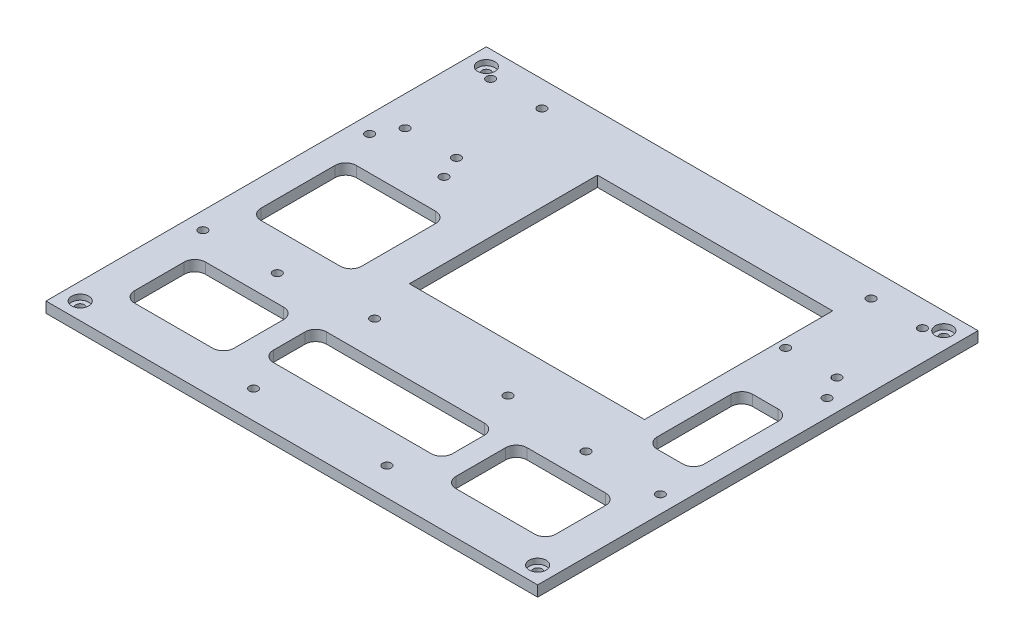
SolidWorks part; units mm, degrees
material "Custom Plastic"
ref_plane "Front Plane" through (0, 0, 0) normal (0, 0, 1) x (1, 0, 0)
ref_plane "Top Plane" through (0, 0, 0) normal (0, 1, 0) x (1, 0, 0)
ref_plane "Right Plane" through (0, 0, 0) normal (1, 0, 0) x (0, 0, -1)
sketch "Sketch1" plane through (0, 0, 0) normal (0, 1, 0) x (1, 0, 0)
  line L1 (-59.5, -51.5) -> (59.5, -51.5)
  line L2 (-59.5, -51.5) -> (-59.5, 51.5)
  line L3 (-59.5, 51.5) -> (59.5, 51.5)
  line L4 (59.5, -51.5) -> (59.5, 51.5)
  line L5 (-59.5, -51.5) -> (59.5, 51.5) construction
  line L6 (-59.5, 51.5) -> (59.5, -51.5) construction
  point P0 (0, 0)
  dimension "D1" = 119
  dimension "D2" = 103
extrude "Boss-Extrude1" add sketch "Sketch1" along normal blind 2.5
sketch "Sketch3" plane through (0, 2.5, 0) normal (0, 1, 0) x (1, 0, 0)
  line L0 (-59.5, -51.5) -> (59.5, -51.5) construction
  line L1 (-18.5, -5.5) -> (36.5, -5.5)
  line L2 (-18.5, -5.5) -> (-18.5, 38.5)
  line L3 (-18.5, 38.5) -> (36.5, 38.5)
  line L4 (36.5, -5.5) -> (36.5, 38.5)
  line L5 (-18.5, -5.5) -> (36.5, 38.5) construction
  line L6 (-18.5, 38.5) -> (36.5, -5.5) construction
  line L7 (-59.5, 51.5) -> (-59.5, -51.5) construction
  point P0 (9, 16.5)
  dimension "D1" = 46
  dimension "D2" = 41
  dimension "D3" = 44
  dimension "D4" = 55
extrude "Cut-Extrude2" cut sketch "Sketch3" against normal blind 10
sketch "Sketch4" plane through (-59.5, 0, 0) normal (-1, 0, 0) x (0, 0, 1)
  line L4 (-51.5, 0) -> (51.5, 0)
  line L5 (51.5, 0) -> (51.5, 2.5)
  line L6 (51.5, 2.5) -> (-51.5, 2.5)
  line L7 (-51.5, 2.5) -> (-51.5, 0)
  line L8 (-51.5, 0) -> (51.5, 0)
  line L9 (51.5, 0) -> (51.5, 2.5)
  line L10 (51.5, 2.5) -> (-51.5, 2.5)
  line L11 (-51.5, 2.5) -> (-51.5, 0)
  dimension "D1" = 0
extrude "Boss-Extrude2" add sketch "Sketch4" along normal blind 1.5
sketch "Sketch5" plane through (59.5, 0, 0) normal (1, 0, 0) x (0, 0, -1)
  line L4 (-51.5, 0) -> (51.5, 0)
  line L5 (51.5, 0) -> (51.5, 2.5)
  line L6 (51.5, 2.5) -> (-51.5, 2.5)
  line L7 (-51.5, 2.5) -> (-51.5, 0)
  line L8 (-51.5, 0) -> (51.5, 0)
  line L9 (51.5, 0) -> (51.5, 2.5)
  line L10 (51.5, 2.5) -> (-51.5, 2.5)
  line L11 (-51.5, 2.5) -> (-51.5, 0)
  dimension "D1" = 0
extrude "Boss-Extrude3" add sketch "Sketch5" along normal blind 1.5
sketch "Sketch6" plane through (-61, 0, 0) normal (-1, 0, 0) x (0, 0, 1)
  line L4 (-51.5, 2.5) -> (-51.5, 0)
  line L5 (-51.5, 0) -> (51.5, 0)
  line L6 (51.5, 0) -> (51.5, 2.5)
  line L7 (51.5, 2.5) -> (-51.5, 2.5)
  line L8 (-51.5, 2.5) -> (-51.5, 0)
  line L9 (-51.5, 0) -> (51.5, 0)
  line L10 (51.5, 0) -> (51.5, 2.5)
  line L11 (51.5, 2.5) -> (-51.5, 2.5)
  dimension "D1" = 0
extrude "Cut-Extrude3" cut sketch "Sketch6" against normal blind 3.5
sketch "Sketch7" plane through (61, 0, 0) normal (1, 0, 0) x (0, 0, -1)
  line L4 (-51.5, 2.5) -> (-51.5, 0)
  line L5 (-51.5, 0) -> (51.5, 0)
  line L6 (51.5, 0) -> (51.5, 2.5)
  line L7 (51.5, 2.5) -> (-51.5, 2.5)
  line L8 (-51.5, 2.5) -> (-51.5, 0)
  line L9 (-51.5, 0) -> (51.5, 0)
  line L10 (51.5, 0) -> (51.5, 2.5)
  line L11 (51.5, 2.5) -> (-51.5, 2.5)
  dimension "D1" = 0
extrude "Cut-Extrude4" cut sketch "Sketch7" against normal blind 3.5
sketch "Sketch8" plane through (0, 2.5, 0) normal (0, 1, 0) x (1, 0, 0)
  line L0 (-57.5, -51.5) -> (-57.5, 51.5) construction
  line L1 (-57.5, -51.5) -> (57.5, -51.5) construction
  line L3 (0, 59.9293) -> (0, -77.2132) construction
  circle A0 centre (-15.5, -44.96) radius 1
  circle A1 centre (15.7, -44.96) radius 1
  circle A2 centre (-15.5, -16.63) radius 1
  circle A3 centre (15.7, -16.63) radius 1
  circle A4 centre (-53.5, -18.81) radius 1
  circle A5 centre (-36.1, -18.81) radius 1
  circle A6 centre (-53.5, 20.19) radius 1
  circle A7 centre (-36.1, 20.19) radius 1
  circle A8 centre (36.1, -18.81) radius 1
  circle A9 centre (53.5, -18.81) radius 1
  circle A10 centre (53.5, 20.19) radius 1
  dimension "D1" = 2
  dimension "D2" = 2
  dimension "D7" = 2
  dimension "D8" = 2
  dimension "D13" = 2
  dimension "D14" = 2
  dimension "D15" = 2
  dimension "D16" = 2
  dimension "D3" = 42
  dimension "D4" = 31.2
  dimension "D5" = 6.54
  dimension "D6" = 6.54
  dimension "D9" = 28.33
  dimension "D10" = 28.33
  dimension "D11" = 32.69
  dimension "D12" = 4
  dimension "D17" = 4
  dimension "D18" = 39
  dimension "D19" = 17.4
extrude "Cut-Extrude5" cut sketch "Sketch8" against normal blind 10
sketch "Sketch9" plane through (0, 2.5, 0) normal (0, 1, 0) x (1, 0, 0)
  line L0 (-57.5, -51.5) -> (-57.5, 51.5) construction
  line L1 (57.5, 51.5) -> (-57.5, 51.5) construction
  circle A0 centre (-53.5, 47.5) radius 1
  circle A1 centre (53.5, -47.5) radius 1
  circle A2 centre (53.5, 47.5) radius 1
  circle A3 centre (-53.5, -47.5) radius 1
  point P10 (0, 0)
  dimension "D3" = 2
  dimension "D5" = 2
  dimension "D6" = 2
  dimension "D1" = 4
  dimension "D2" = 4
  dimension "D4" = 2
extrude "Cut-Extrude6" cut sketch "Sketch9" against normal blind 10
sketch "Sketch10" plane through (0, 2.5, 0) normal (0, 1, 0) x (1, 0, 0)
  circle A0 centre (-53.5, 47.5) radius 2
  circle A1 centre (-53.5, -47.5) radius 2
  circle A2 centre (53.5, -47.5) radius 2
  circle A3 centre (53.5, 47.5) radius 2
  dimension "D1" = 4
  dimension "D2" = 4
  dimension "D3" = 4
  dimension "D4" = 4
extrude "Cut-Extrude7" cut sketch "Sketch10" against normal blind 1.25
sketch "Sketch11" plane through (0, 2.5, 0) normal (0, 1, 0) x (1, 0, 0)
  line L0 (-57.5, 51.5) -> (-57.5, -51.5) construction
  line L1 (-57.5, -51.5) -> (-57.5, 51.5) construction
  line L2 (57.5, 51.5) -> (-57.5, 51.5) construction
  line L4 (0, 60.3804) -> (0, 0) construction
  circle A0 centre (-50.5, 45.5) radius 1
  circle A1 centre (-50.5, 25.5) radius 1
  circle A2 centre (-38.5, 45.5) radius 1
  circle A3 centre (-38.5, 25.5) radius 1
  circle A4 centre (50.5, 25.5) radius 1
  circle A5 centre (38.5, 25.5) radius 1
  circle A6 centre (38.5, 45.5) radius 1
  circle A7 centre (50.5, 45.5) radius 1
  dimension "D1" = 2
  dimension "D2" = 2
  dimension "D3" = 2
  dimension "D4" = 2
  dimension "D5" = 7
  dimension "D6" = 7
  dimension "D7" = 12
  dimension "D9" = 6
  dimension "D10" = 20
extrude "Cut-Extrude8" cut sketch "Sketch11" against normal blind 11
sketch "Sketch12" plane through (0, 2.5, 0) normal (0, 1, 0) x (1, 0, 0)
  line L0 (-46.7391, -24.9455) -> (-28.4571, -24.9455)
  line L1 (-48.6757, -10.0359) -> (-30.1363, -10.0359)
  line L2 (-51.1757, -7.5359) -> (-51.1757, 9.7595)
  line L3 (-48.6757, 12.2595) -> (-30.1363, 12.2595)
  line L4 (-27.6363, -7.5359) -> (-27.6363, 9.7595)
  line L5 (-51.1757, -10.0359) -> (-27.6363, 12.2595) construction
  line L6 (-51.1757, 12.2595) -> (-27.6363, -10.0359) construction
  line L7 (-25.9571, -27.4455) -> (-25.9571, -39.0653)
  line L8 (-28.4571, -41.5653) -> (-46.7391, -41.5653)
  line L9 (-49.2391, -39.0653) -> (-49.2391, -27.4455)
  line L10 (-20.9571, -27.4455) -> (-20.9571, -34.8668)
  line L11 (-18.4571, -37.3668) -> (18.4571, -37.3668)
  line L12 (20.9571, -34.8668) -> (20.9571, -27.4455)
  line L13 (18.4571, -24.9455) -> (-18.4571, -24.9455)
  line L14 (28.4571, -41.5653) -> (46.8503, -41.5653)
  line L15 (49.3503, -39.0653) -> (49.3503, -27.4455)
  line L16 (46.8503, -24.9455) -> (28.4571, -24.9455)
  line L17 (25.9571, -27.4455) -> (25.9571, -39.0653)
  line L18 (0, 20.449) -> (0, -71.2445) construction
  line L19 (41.5, 9.7595) -> (41.5, -7.5359)
  line L20 (44, -10.0359) -> (50, -10.0359)
  line L21 (52.5, -7.5359) -> (52.5, 9.7595)
  line L22 (50, 12.2595) -> (44, 12.2595)
  line L23 (57.5, 51.5) -> (57.5, -51.5) construction
  line L24 (36.5, -5.5) -> (36.5, 38.5) construction
  arc A0 (52.5, 9.7595) -> (50, 12.2595) centre (50, 9.7595) ccw
  arc A1 (50, -10.0359) -> (52.5, -7.5359) centre (50, -7.5359) ccw
  arc A2 (41.5, -7.5359) -> (44, -10.0359) centre (44, -7.5359) ccw
  arc A3 (41.5, 9.7595) -> (44, 12.2595) centre (44, 9.7595) cw
  arc A4 (49.3503, -27.4455) -> (46.8503, -24.9455) centre (46.8503, -27.4455) ccw
  arc A5 (46.8503, -41.5653) -> (49.3503, -39.0653) centre (46.8503, -39.0653) ccw
  arc A6 (28.4571, -41.5653) -> (25.9571, -39.0653) centre (28.4571, -39.0653) cw
  arc A7 (28.4571, -24.9455) -> (25.9571, -27.4455) centre (28.4571, -27.4455) ccw
  arc A8 (20.9571, -27.4455) -> (18.4571, -24.9455) centre (18.4571, -27.4455) ccw
  arc A9 (18.4571, -37.3668) -> (20.9571, -34.8668) centre (18.4571, -34.8668) ccw
  arc A10 (-20.9571, -34.8668) -> (-18.4571, -37.3668) centre (-18.4571, -34.8668) ccw
  arc A11 (-20.9571, -27.4455) -> (-18.4571, -24.9455) centre (-18.4571, -27.4455) cw
  arc A12 (-28.4571, -24.9455) -> (-25.9571, -27.4455) centre (-28.4571, -27.4455) cw
  arc A13 (-25.9571, -39.0653) -> (-28.4571, -41.5653) centre (-28.4571, -39.0653) cw
  arc A14 (-46.7391, -41.5653) -> (-49.2391, -39.0653) centre (-46.7391, -39.0653) cw
  arc A15 (-46.7391, -24.9455) -> (-49.2391, -27.4455) centre (-46.7391, -27.4455) ccw
  arc A16 (-30.1363, 12.2595) -> (-27.6363, 9.7595) centre (-30.1363, 9.7595) cw
  arc A17 (-30.1363, -10.0359) -> (-27.6363, -7.5359) centre (-30.1363, -7.5359) ccw
  arc A18 (-48.6757, -10.0359) -> (-51.1757, -7.5359) centre (-48.6757, -7.5359) cw
  arc A19 (-51.1757, 9.7595) -> (-48.6757, 12.2595) centre (-48.6757, 9.7595) cw
  point P0 (-39.406, 1.1118)
  point P19 (0, -24.9455)
  point P23 (52.5, 1.1118)
  dimension "D5" = 2.5
  dimension "D1" = 5
  dimension "D2" = 5
  dimension "D3" = 5
  dimension "D4" = 5
extrude "Cut-Extrude9" cut sketch "Sketch12" against normal blind 11
